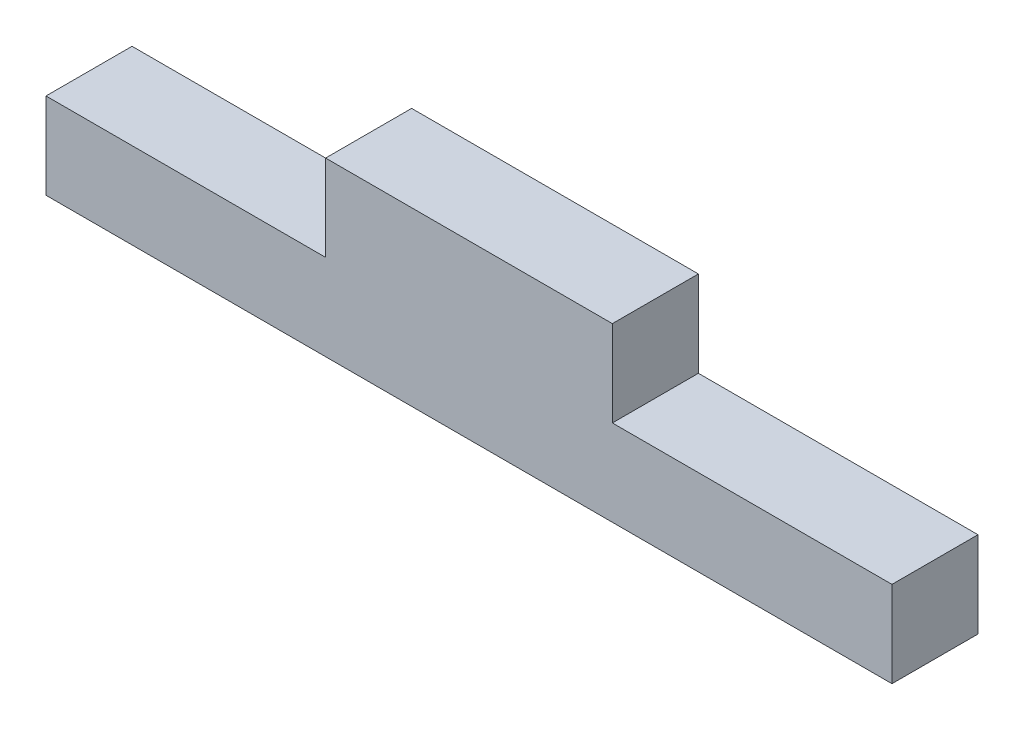
SolidWorks part; units mm, degrees
ref_plane "Plano frontal" through (0, 0, 0) normal (0, 0, 1) x (1, 0, 0)
ref_plane "Plano superior" through (0, 0, 0) normal (0, 1, 0) x (1, 0, 0)
ref_plane "Plano direito" through (0, 0, 0) normal (1, 0, 0) x (0, 0, -1)
sketch "Esboço1" plane through (0, 0, 0) normal (0, 0, 1) x (1, 0, 0)
  line L0 (0, 6) -> (19.5, 6)
  line L1 (0, 0) -> (59, 0)
  line L2 (0, 0) -> (0, 12)
  line L3 (0, 12) -> (59, 12)
  line L4 (59, 0) -> (59, 12)
  line L5 (0, 12) -> (6, 12)
  line L6 (0, 12) -> (0, 6)
  line L9 (59, 12) -> (53, 12)
  line L10 (59, 12) -> (59, 6)
  line L13 (19.5, 6) -> (19.5, 12)
  line L14 (59, 6) -> (39.5, 6)
  line L15 (39.5, 6) -> (39.5, 12)
  dimension "D1" = 12
  dimension "D2" = 59
  dimension "D3" = 6
  dimension "D4" = 19.5
  dimension "D5" = 19.5
extrude "Ressalto-extrusão1" add sketch "Esboço1" along normal blind 6
